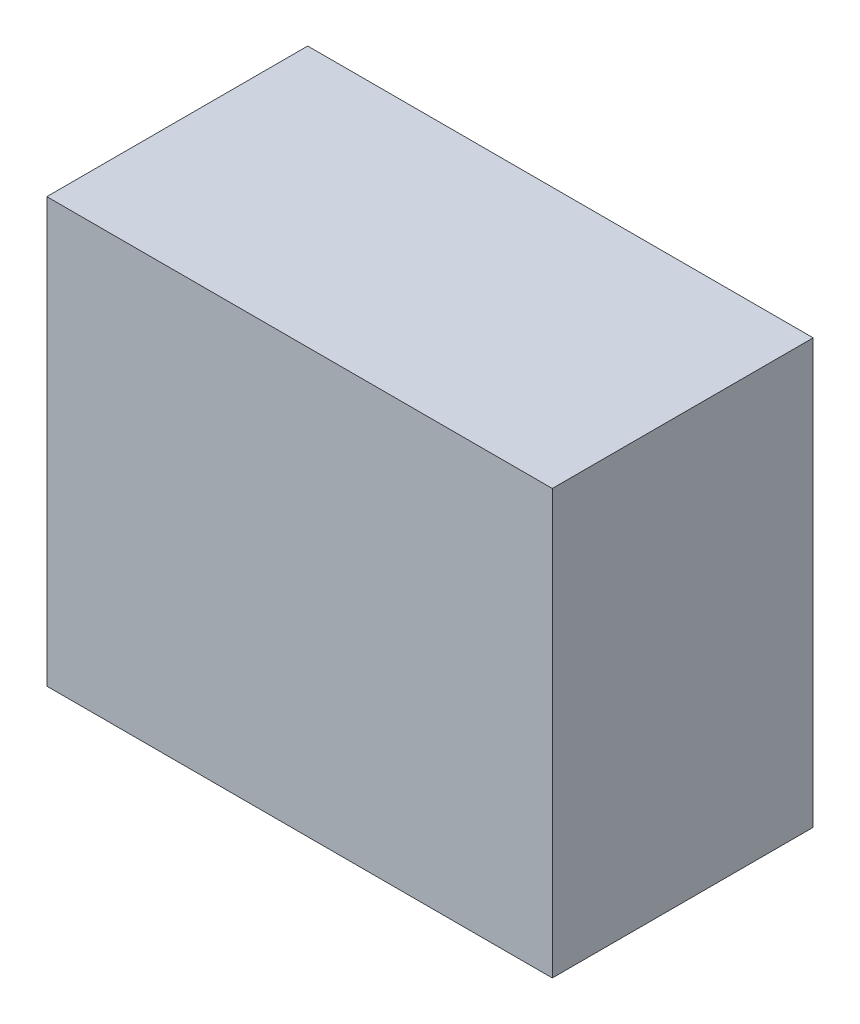
SolidWorks part; units mm, degrees
ref_plane "Front Plane" through (0, 0, 0) normal (0, 0, 1) x (1, 0, 0)
ref_plane "Top Plane" through (0, 0, 0) normal (0, 1, 0) x (1, 0, 0)
ref_plane "Right Plane" through (0, 0, 0) normal (1, 0, 0) x (0, 0, -1)
sketch "Sketch1" plane through (0, 0, 0) normal (0, 0, 1) x (1, 0, 0)
  line L5 (0, 0) -> (155, 0)
  line L6 (155, 0) -> (155, 130)
  line L7 (155, 130) -> (0, 130)
  line L8 (0, 130) -> (0, 0)
  line L9 (0, 0) -> (155, 0)
  line L10 (155, 0) -> (155, 130)
  line L11 (155, 130) -> (0, 130)
  line L12 (0, 130) -> (0, 0)
  dimension "D1" = 0
extrude "Boss-Extrude1" add sketch "Sketch1" along normal blind 80
